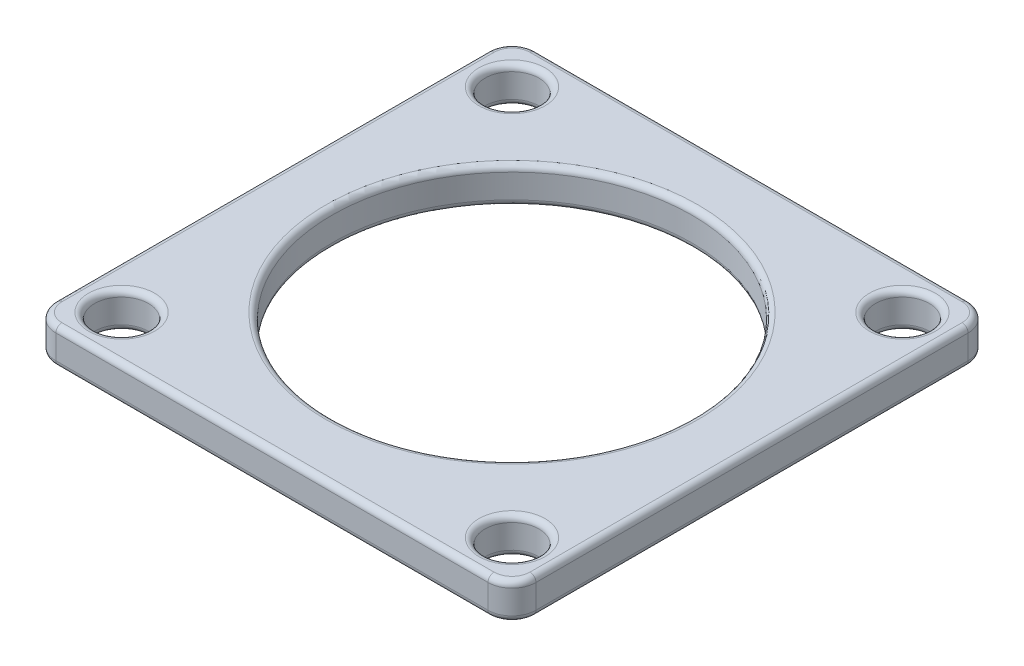
SolidWorks part; units mm, degrees
ref_plane "Front Plane" through (0, 0, 0) normal (0, 0, 1) x (1, 0, 0)
ref_plane "Top Plane" through (0, 0, 0) normal (0, 1, 0) x (1, 0, 0)
ref_plane "Right Plane" through (0, 0, 0) normal (1, 0, 0) x (0, 0, -1)
sketch "Sketch1" plane through (0, 0, 0) normal (0, 1, 0) x (1, 0, 0)
  line L0 (-20, 0) -> (20, 0) construction
  line L1 (-18, 20) -> (18, 20)
  line L2 (-20, 18) -> (-20, -18)
  line L3 (-18, -20) -> (18, -20)
  line L4 (20, 18) -> (20, -18)
  line L5 (-20, 20) -> (20, -20) construction
  line L6 (-20, -20) -> (20, 20) construction
  circle A0 centre (0, 0) radius 23 construction
  circle A1 centre (-16.2635, 16.2635) radius 2.25
  circle A2 centre (16.2635, 16.2635) radius 2.25
  circle A3 centre (16.2635, -16.2635) radius 2.25
  circle A4 centre (-16.2635, -16.2635) radius 2.25
  circle A5 centre (0, 0) radius 15
  arc A6 (20, -18) -> (18, -20) centre (18, -18) cw
  arc A7 (-18, -20) -> (-20, -18) centre (-18, -18) cw
  arc A8 (20, 18) -> (18, 20) centre (18, 18) ccw
  arc A9 (-18, 20) -> (-20, 18) centre (-18, 18) ccw
  point P0 (0, 0)
  dimension "D3" = 46
  dimension "D4" = 2
  dimension "D5" = 30
  dimension "D1" = 40
  dimension "D2" = 40
extrude "Boss-Extrude1" add sketch "Sketch1" along normal blind 3
fillet "Fillet1" radius 0.5 26 edges at (0, 0, 15) (-16.2635, 0, 14.0135) (16.2635, 0, 14.0135) (16.2635, 0, -14.0135) (-16.2635, 0, -14.0135) (0, 0, -20) (-20, 0, 0) (0, 0, 20) (20, 0, 0) (0, 3, 15) (16.2635, 3, 14.0135) (-16.2635, 3, -14.0135) (0, 3, 20) (-20, 3, 0) (0, 3, -20) (20, 3, 0) (16.2635, 3, -14.0135) (-16.2635, 3, 14.0135) (19.4142, 0, -19.4142) (-19.4142, 0, -19.4142) (-19.4142, 0, 19.4142) (19.4142, 0, 19.4142) (-19.4142, 3, 19.4142) (-19.4142, 3, -19.4142) (19.4142, 3, -19.4142) (19.4142, 3, 19.4142)
